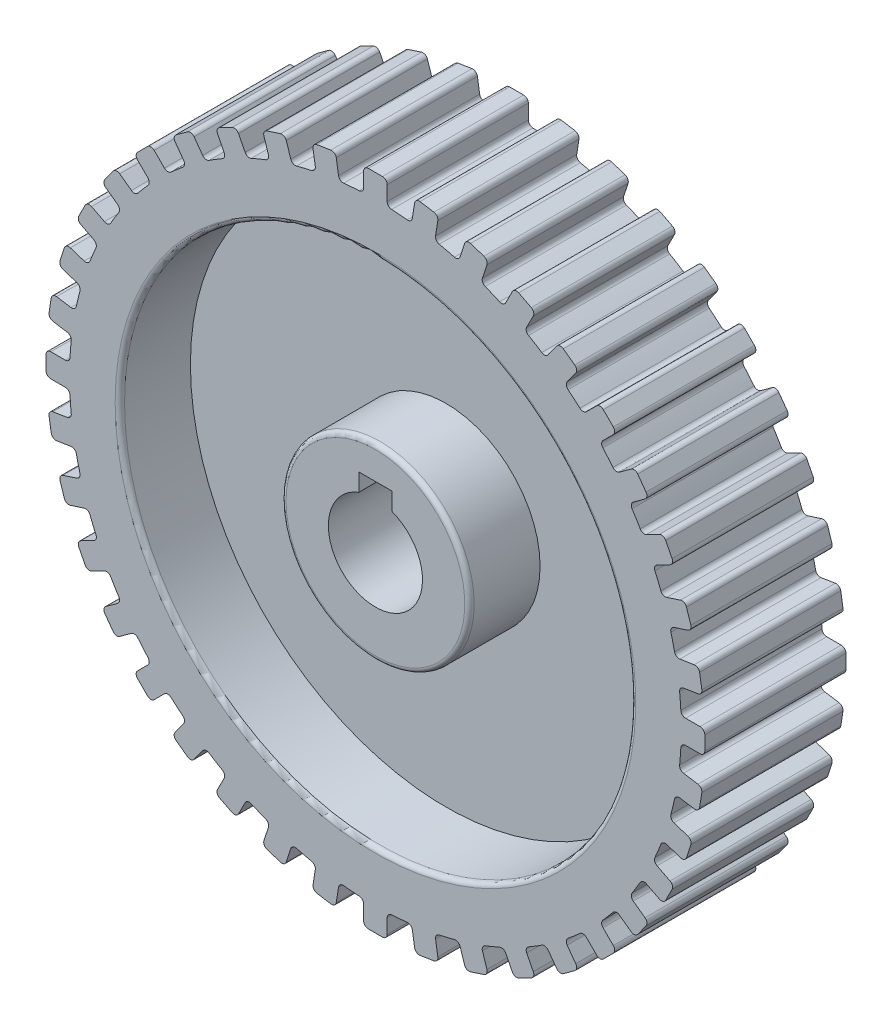
SolidWorks part; units mm, degrees
ref_plane "Front Plane" through (0, 0, 0) normal (0, 0, 1) x (1, 0, 0)
ref_plane "Top Plane" through (0, 0, 0) normal (0, 1, 0) x (1, 0, 0)
ref_plane "Right Plane" through (0, 0, 0) normal (1, 0, 0) x (0, 0, -1)
sketch "Sketch1" plane through (0, 0, 0) normal (0, 0, 1) x (1, 0, 0)
  line L0 (8.3248, 68.5416) -> (7.8409, 65.4868)
  line L1 (-1.5, 70) -> (1.5, 70)
  line L2 (2.5, 69) -> (2.5, 65.9071)
  line L3 (-2.5, 69) -> (-2.5, 65.9071)
  line L4 (9.4689, 69.3728) -> (12.4319, 68.9035)
  line L5 (13.2632, 67.7594) -> (12.7794, 64.7046)
  line L6 (18.9445, 66.3954) -> (17.9888, 63.4539)
  line L7 (20.2046, 67.0375) -> (23.0578, 66.1104)
  line L8 (23.6998, 64.8504) -> (22.7441, 61.9089)
  line L9 (29.0978, 62.6144) -> (27.6937, 59.8587)
  line L10 (30.4428, 63.0514) -> (33.1158, 61.6895)
  line L11 (33.5529, 60.3445) -> (32.1487, 57.5887)
  line L12 (38.5346, 57.2916) -> (36.7167, 54.7895)
  line L13 (39.9314, 57.5129) -> (42.3585, 55.7495)
  line L14 (42.5797, 54.3527) -> (40.7618, 51.8505)
  line L15 (47.0226, 50.5581) -> (44.8356, 48.3711)
  line L16 (48.4368, 50.5581) -> (50.5581, 48.4368)
  line L17 (50.5581, 47.0226) -> (48.3711, 44.8356)
  line L18 (54.3527, 42.5797) -> (51.8505, 40.7618)
  line L19 (55.7495, 42.3585) -> (57.5129, 39.9314)
  line L20 (57.2916, 38.5346) -> (54.7895, 36.7167)
  line L21 (60.3445, 33.5529) -> (57.5887, 32.1487)
  line L22 (61.6895, 33.1158) -> (63.0514, 30.4428)
  line L23 (62.6144, 29.0978) -> (59.8587, 27.6937)
  line L24 (64.8504, 23.6998) -> (61.9089, 22.7441)
  line L25 (66.1104, 23.0578) -> (67.0375, 20.2046)
  line L26 (66.3954, 18.9445) -> (63.4539, 17.9888)
  line L27 (67.7594, 13.2632) -> (64.7046, 12.7794)
  line L28 (68.9035, 12.4319) -> (69.3728, 9.4689)
  line L29 (68.5416, 8.3248) -> (65.4868, 7.8409)
  line L30 (69, 2.5) -> (65.9071, 2.5)
  line L31 (70, 1.5) -> (70, -1.5)
  line L32 (69, -2.5) -> (65.9071, -2.5)
  line L33 (68.5416, -8.3248) -> (65.4868, -7.8409)
  line L34 (69.3728, -9.4689) -> (68.9035, -12.4319)
  line L35 (67.7594, -13.2632) -> (64.7046, -12.7794)
  line L36 (66.3954, -18.9445) -> (63.4539, -17.9888)
  line L37 (67.0375, -20.2046) -> (66.1104, -23.0578)
  line L38 (64.8504, -23.6998) -> (61.9089, -22.7441)
  line L39 (62.6144, -29.0978) -> (59.8587, -27.6937)
  line L40 (63.0514, -30.4428) -> (61.6895, -33.1158)
  line L41 (60.3445, -33.5529) -> (57.5887, -32.1487)
  line L42 (57.2916, -38.5346) -> (54.7895, -36.7167)
  line L43 (57.5129, -39.9314) -> (55.7495, -42.3585)
  line L44 (54.3527, -42.5797) -> (51.8505, -40.7618)
  line L45 (50.5581, -47.0226) -> (48.3711, -44.8356)
  line L46 (50.5581, -48.4368) -> (48.4368, -50.5581)
  line L47 (47.0226, -50.5581) -> (44.8356, -48.3711)
  line L48 (42.5797, -54.3527) -> (40.7618, -51.8505)
  line L49 (42.3585, -55.7495) -> (39.9314, -57.5129)
  line L50 (38.5346, -57.2916) -> (36.7167, -54.7895)
  line L51 (33.5529, -60.3445) -> (32.1487, -57.5887)
  line L52 (33.1158, -61.6895) -> (30.4428, -63.0514)
  line L53 (29.0978, -62.6144) -> (27.6937, -59.8587)
  line L54 (23.6998, -64.8504) -> (22.7441, -61.9089)
  line L55 (23.0578, -66.1104) -> (20.2046, -67.0375)
  line L56 (18.9445, -66.3954) -> (17.9888, -63.4539)
  line L57 (13.2632, -67.7594) -> (12.7794, -64.7046)
  line L58 (12.4319, -68.9035) -> (9.4689, -69.3728)
  line L59 (8.3248, -68.5416) -> (7.8409, -65.4868)
  line L60 (2.5, -69) -> (2.5, -65.9071)
  line L61 (1.5, -70) -> (-1.5, -70)
  line L62 (-2.5, -69) -> (-2.5, -65.9071)
  line L63 (-8.3248, -68.5416) -> (-7.8409, -65.4868)
  line L64 (-9.4689, -69.3728) -> (-12.4319, -68.9035)
  line L65 (-13.2632, -67.7594) -> (-12.7794, -64.7046)
  line L66 (-18.9445, -66.3954) -> (-17.9888, -63.4539)
  line L67 (-20.2046, -67.0375) -> (-23.0578, -66.1104)
  line L68 (-23.6998, -64.8504) -> (-22.7441, -61.9089)
  line L69 (-29.0978, -62.6144) -> (-27.6937, -59.8587)
  line L70 (-30.4428, -63.0514) -> (-33.1158, -61.6895)
  line L71 (-33.5529, -60.3445) -> (-32.1487, -57.5887)
  line L72 (-38.5346, -57.2916) -> (-36.7167, -54.7895)
  line L73 (-39.9314, -57.5129) -> (-42.3585, -55.7495)
  line L74 (-42.5797, -54.3527) -> (-40.7618, -51.8505)
  line L75 (-47.0226, -50.5581) -> (-44.8356, -48.3711)
  line L76 (-48.4368, -50.5581) -> (-50.5581, -48.4368)
  line L77 (-50.5581, -47.0226) -> (-48.3711, -44.8356)
  line L78 (-54.3527, -42.5797) -> (-51.8505, -40.7618)
  line L79 (-55.7495, -42.3585) -> (-57.5129, -39.9314)
  line L80 (-57.2916, -38.5346) -> (-54.7895, -36.7167)
  line L81 (-60.3445, -33.5529) -> (-57.5887, -32.1487)
  line L82 (-61.6895, -33.1158) -> (-63.0514, -30.4428)
  line L83 (-62.6144, -29.0978) -> (-59.8587, -27.6937)
  line L84 (-64.8504, -23.6998) -> (-61.9089, -22.7441)
  line L85 (-66.1104, -23.0578) -> (-67.0375, -20.2046)
  line L86 (-66.3954, -18.9445) -> (-63.4539, -17.9888)
  line L87 (-67.7594, -13.2632) -> (-64.7046, -12.7794)
  line L88 (-68.9035, -12.4319) -> (-69.3728, -9.4689)
  line L89 (-68.5416, -8.3248) -> (-65.4868, -7.8409)
  line L90 (-69, -2.5) -> (-65.9071, -2.5)
  line L91 (-70, -1.5) -> (-70, 1.5)
  line L92 (-69, 2.5) -> (-65.9071, 2.5)
  line L93 (-68.5416, 8.3248) -> (-65.4868, 7.8409)
  line L94 (-69.3728, 9.4689) -> (-68.9035, 12.4319)
  line L95 (-67.7594, 13.2632) -> (-64.7046, 12.7794)
  line L96 (-66.3954, 18.9445) -> (-63.4539, 17.9888)
  line L97 (-67.0375, 20.2046) -> (-66.1104, 23.0578)
  line L98 (-64.8504, 23.6998) -> (-61.9089, 22.7441)
  line L99 (-62.6144, 29.0978) -> (-59.8587, 27.6937)
  line L100 (-63.0514, 30.4428) -> (-61.6895, 33.1158)
  line L101 (-60.3445, 33.5529) -> (-57.5887, 32.1487)
  line L102 (-57.2916, 38.5346) -> (-54.7895, 36.7167)
  line L103 (-57.5129, 39.9314) -> (-55.7495, 42.3585)
  line L104 (-54.3527, 42.5797) -> (-51.8505, 40.7618)
  line L105 (-50.5581, 47.0226) -> (-48.3711, 44.8356)
  line L106 (-50.5581, 48.4368) -> (-48.4368, 50.5581)
  line L107 (-47.0226, 50.5581) -> (-44.8356, 48.3711)
  line L108 (-42.5797, 54.3527) -> (-40.7618, 51.8505)
  line L109 (-42.3585, 55.7495) -> (-39.9314, 57.5129)
  line L110 (-38.5346, 57.2916) -> (-36.7167, 54.7895)
  line L111 (-33.5529, 60.3445) -> (-32.1487, 57.5887)
  line L112 (-33.1158, 61.6895) -> (-30.4428, 63.0514)
  line L113 (-29.0978, 62.6144) -> (-27.6937, 59.8587)
  line L114 (-23.6998, 64.8504) -> (-22.7441, 61.9089)
  line L115 (-23.0578, 66.1104) -> (-20.2046, 67.0375)
  line L116 (-18.9445, 66.3954) -> (-17.9888, 63.4539)
  line L117 (-13.2632, 67.7594) -> (-12.7794, 64.7046)
  line L118 (-12.4319, 68.9035) -> (-9.4689, 69.3728)
  line L119 (-8.3248, 68.5416) -> (-7.8409, 65.4868)
  arc A0 (-3.447, 64.9085) -> (-6.7494, 64.6486) centre (0, 0) ccw
  arc A2 (-2.5, 65.9071) -> (-3.447, 64.9085) centre (-3.5, 65.9071) cw
  arc A3 (3.447, 64.9085) -> (2.5, 65.9071) centre (3.5, 65.9071) cw
  arc A4 (1.5, 70) -> (2.5, 69) centre (1.5, 69) cw
  arc A5 (-1.5, 70) -> (-2.5, 69) centre (-1.5, 69) ccw
  arc A6 (7.8409, 65.4868) -> (6.7494, 64.6486) centre (6.8532, 65.6432) cw
  arc A7 (9.4689, 69.3728) -> (8.3248, 68.5416) centre (9.3124, 68.3851) ccw
  arc A8 (12.4319, 68.9035) -> (13.2632, 67.7594) centre (12.2755, 67.9158) cw
  arc A9 (13.5585, 63.5702) -> (12.7794, 64.7046) centre (13.7671, 64.5482) cw
  arc A10 (17.9888, 63.4539) -> (16.7796, 62.7969) centre (17.0377, 63.763) cw
  arc A11 (20.2046, 67.0375) -> (18.9445, 66.3954) centre (19.8956, 66.0864) ccw
  arc A12 (23.0578, 66.1104) -> (23.6998, 64.8504) centre (22.7488, 65.1594) cw
  arc A13 (23.3361, 60.6665) -> (22.7441, 61.9089) centre (23.6951, 61.5998) cw
  arc A14 (27.6937, 59.8587) -> (26.3966, 59.3988) centre (26.8027, 60.3127) cw
  arc A15 (30.4428, 63.0514) -> (29.0978, 62.6144) centre (29.9888, 62.1604) ccw
  arc A16 (33.1158, 61.6895) -> (33.5529, 60.3445) centre (32.6619, 60.7985) cw
  arc A17 (32.5391, 56.269) -> (32.1487, 57.5887) centre (33.0397, 57.1347) cw
  arc A18 (36.7167, 54.7895) -> (35.3636, 54.5382) centre (35.9077, 55.3772) cw
  arc A19 (39.9314, 57.5129) -> (38.5346, 57.2916) centre (39.3437, 56.7039) ccw
  arc A20 (42.3585, 55.7495) -> (42.5797, 54.3527) centre (41.7707, 54.9405) cw
  arc A21 (40.9409, 50.486) -> (40.7618, 51.8505) centre (41.5708, 51.2627) cw
  arc A22 (44.8356, 48.3711) -> (43.4599, 48.3346) centre (44.1285, 49.0783) cw
  arc A23 (48.4368, 50.5581) -> (47.0226, 50.5581) centre (47.7297, 49.851) ccw
  arc A24 (50.5581, 48.4368) -> (50.5581, 47.0226) centre (49.851, 47.7297) cw
  arc A25 (48.3346, 43.4599) -> (48.3711, 44.8356) centre (49.0783, 44.1285) cw
  arc A26 (51.8505, 40.7618) -> (50.486, 40.9409) centre (51.2627, 41.5708) cw
  arc A27 (55.7495, 42.3585) -> (54.3527, 42.5797) centre (54.9405, 41.7707) ccw
  arc A28 (57.5129, 39.9314) -> (57.2916, 38.5346) centre (56.7039, 39.3437) cw
  arc A29 (54.5382, 35.3636) -> (54.7895, 36.7167) centre (55.3772, 35.9077) cw
  arc A30 (57.5887, 32.1487) -> (56.269, 32.5391) centre (57.1347, 33.0397) cw
  arc A31 (61.6895, 33.1158) -> (60.3445, 33.5529) centre (60.7985, 32.6619) ccw
  arc A32 (63.0514, 30.4428) -> (62.6144, 29.0978) centre (62.1604, 29.9888) cw
  arc A33 (59.3988, 26.3966) -> (59.8587, 27.6937) centre (60.3127, 26.8027) cw
  arc A34 (61.9089, 22.7441) -> (60.6665, 23.3361) centre (61.5998, 23.6951) cw
  arc A35 (66.1104, 23.0578) -> (64.8504, 23.6998) centre (65.1594, 22.7488) ccw
  arc A36 (67.0375, 20.2046) -> (66.3954, 18.9445) centre (66.0864, 19.8956) cw
  arc A37 (62.7969, 16.7796) -> (63.4539, 17.9888) centre (63.763, 17.0377) cw
  arc A38 (64.7046, 12.7794) -> (63.5702, 13.5585) centre (64.5482, 13.7671) cw
  arc A39 (68.9035, 12.4319) -> (67.7594, 13.2632) centre (67.9158, 12.2755) ccw
  arc A40 (69.3728, 9.4689) -> (68.5416, 8.3248) centre (68.3851, 9.3124) cw
  arc A41 (64.6486, 6.7494) -> (65.4868, 7.8409) centre (65.6432, 6.8532) cw
  arc A42 (65.9071, 2.5) -> (64.9085, 3.447) centre (65.9071, 3.5) cw
  arc A43 (70, 1.5) -> (69, 2.5) centre (69, 1.5) ccw
  arc A44 (70, -1.5) -> (69, -2.5) centre (69, -1.5) cw
  arc A45 (64.9085, -3.447) -> (65.9071, -2.5) centre (65.9071, -3.5) cw
  arc A46 (65.4868, -7.8409) -> (64.6486, -6.7494) centre (65.6432, -6.8532) cw
  arc A47 (69.3728, -9.4689) -> (68.5416, -8.3248) centre (68.3851, -9.3124) ccw
  arc A48 (68.9035, -12.4319) -> (67.7594, -13.2632) centre (67.9158, -12.2755) cw
  arc A49 (63.5702, -13.5585) -> (64.7046, -12.7794) centre (64.5482, -13.7671) cw
  arc A50 (63.4539, -17.9888) -> (62.7969, -16.7796) centre (63.763, -17.0377) cw
  arc A51 (67.0375, -20.2046) -> (66.3954, -18.9445) centre (66.0864, -19.8956) ccw
  arc A52 (66.1104, -23.0578) -> (64.8504, -23.6998) centre (65.1594, -22.7488) cw
  arc A53 (60.6665, -23.3361) -> (61.9089, -22.7441) centre (61.5998, -23.6951) cw
  arc A54 (59.8587, -27.6937) -> (59.3988, -26.3966) centre (60.3127, -26.8027) cw
  arc A55 (63.0514, -30.4428) -> (62.6144, -29.0978) centre (62.1604, -29.9888) ccw
  arc A56 (61.6895, -33.1158) -> (60.3445, -33.5529) centre (60.7985, -32.6619) cw
  arc A57 (56.269, -32.5391) -> (57.5887, -32.1487) centre (57.1347, -33.0397) cw
  arc A58 (54.7895, -36.7167) -> (54.5382, -35.3636) centre (55.3772, -35.9077) cw
  arc A59 (57.5129, -39.9314) -> (57.2916, -38.5346) centre (56.7039, -39.3437) ccw
  arc A60 (55.7495, -42.3585) -> (54.3527, -42.5797) centre (54.9405, -41.7707) cw
  arc A61 (50.486, -40.9409) -> (51.8505, -40.7618) centre (51.2627, -41.5708) cw
  arc A62 (48.3711, -44.8356) -> (48.3346, -43.4599) centre (49.0783, -44.1285) cw
  arc A63 (50.5581, -48.4368) -> (50.5581, -47.0226) centre (49.851, -47.7297) ccw
  arc A64 (48.4368, -50.5581) -> (47.0226, -50.5581) centre (47.7297, -49.851) cw
  arc A65 (43.4599, -48.3346) -> (44.8356, -48.3711) centre (44.1285, -49.0783) cw
  arc A66 (40.7618, -51.8505) -> (40.9409, -50.486) centre (41.5708, -51.2627) cw
  arc A67 (42.3585, -55.7495) -> (42.5797, -54.3527) centre (41.7707, -54.9405) ccw
  arc A68 (39.9314, -57.5129) -> (38.5346, -57.2916) centre (39.3437, -56.7039) cw
  arc A69 (35.3636, -54.5382) -> (36.7167, -54.7895) centre (35.9077, -55.3772) cw
  arc A70 (32.1487, -57.5887) -> (32.5391, -56.269) centre (33.0397, -57.1347) cw
  arc A71 (33.1158, -61.6895) -> (33.5529, -60.3445) centre (32.6619, -60.7985) ccw
  arc A72 (30.4428, -63.0514) -> (29.0978, -62.6144) centre (29.9888, -62.1604) cw
  arc A73 (26.3966, -59.3988) -> (27.6937, -59.8587) centre (26.8027, -60.3127) cw
  arc A74 (22.7441, -61.9089) -> (23.3361, -60.6665) centre (23.6951, -61.5998) cw
  arc A75 (23.0578, -66.1104) -> (23.6998, -64.8504) centre (22.7488, -65.1594) ccw
  arc A76 (20.2046, -67.0375) -> (18.9445, -66.3954) centre (19.8956, -66.0864) cw
  arc A77 (16.7796, -62.7969) -> (17.9888, -63.4539) centre (17.0377, -63.763) cw
  arc A78 (12.7794, -64.7046) -> (13.5585, -63.5702) centre (13.7671, -64.5482) cw
  arc A79 (12.4319, -68.9035) -> (13.2632, -67.7594) centre (12.2755, -67.9158) ccw
  arc A80 (9.4689, -69.3728) -> (8.3248, -68.5416) centre (9.3124, -68.3851) cw
  arc A81 (6.7494, -64.6486) -> (7.8409, -65.4868) centre (6.8532, -65.6432) cw
  arc A82 (2.5, -65.9071) -> (3.447, -64.9085) centre (3.5, -65.9071) cw
  arc A83 (1.5, -70) -> (2.5, -69) centre (1.5, -69) ccw
  arc A84 (-1.5, -70) -> (-2.5, -69) centre (-1.5, -69) cw
  arc A85 (-3.447, -64.9085) -> (-2.5, -65.9071) centre (-3.5, -65.9071) cw
  arc A86 (-7.8409, -65.4868) -> (-6.7494, -64.6486) centre (-6.8532, -65.6432) cw
  arc A87 (-9.4689, -69.3728) -> (-8.3248, -68.5416) centre (-9.3124, -68.3851) ccw
  arc A88 (-12.4319, -68.9035) -> (-13.2632, -67.7594) centre (-12.2755, -67.9158) cw
  arc A89 (-13.5585, -63.5702) -> (-12.7794, -64.7046) centre (-13.7671, -64.5482) cw
  arc A90 (-17.9888, -63.4539) -> (-16.7796, -62.7969) centre (-17.0377, -63.763) cw
  arc A91 (-20.2046, -67.0375) -> (-18.9445, -66.3954) centre (-19.8956, -66.0864) ccw
  arc A92 (-23.0578, -66.1104) -> (-23.6998, -64.8504) centre (-22.7488, -65.1594) cw
  arc A93 (-23.3361, -60.6665) -> (-22.7441, -61.9089) centre (-23.6951, -61.5998) cw
  arc A94 (-27.6937, -59.8587) -> (-26.3966, -59.3988) centre (-26.8027, -60.3127) cw
  arc A95 (-30.4428, -63.0514) -> (-29.0978, -62.6144) centre (-29.9888, -62.1604) ccw
  arc A96 (-33.1158, -61.6895) -> (-33.5529, -60.3445) centre (-32.6619, -60.7985) cw
  arc A97 (-32.5391, -56.269) -> (-32.1487, -57.5887) centre (-33.0397, -57.1347) cw
  arc A98 (-36.7167, -54.7895) -> (-35.3636, -54.5382) centre (-35.9077, -55.3772) cw
  arc A99 (-39.9314, -57.5129) -> (-38.5346, -57.2916) centre (-39.3437, -56.7039) ccw
  arc A100 (-42.3585, -55.7495) -> (-42.5797, -54.3527) centre (-41.7707, -54.9405) cw
  arc A101 (-40.9409, -50.486) -> (-40.7618, -51.8505) centre (-41.5708, -51.2627) cw
  arc A102 (-44.8356, -48.3711) -> (-43.4599, -48.3346) centre (-44.1285, -49.0783) cw
  arc A103 (-48.4368, -50.5581) -> (-47.0226, -50.5581) centre (-47.7297, -49.851) ccw
  arc A104 (-50.5581, -48.4368) -> (-50.5581, -47.0226) centre (-49.851, -47.7297) cw
  arc A105 (-48.3346, -43.4599) -> (-48.3711, -44.8356) centre (-49.0783, -44.1285) cw
  arc A106 (-51.8505, -40.7618) -> (-50.486, -40.9409) centre (-51.2627, -41.5708) cw
  arc A107 (-55.7495, -42.3585) -> (-54.3527, -42.5797) centre (-54.9405, -41.7707) ccw
  arc A108 (-57.5129, -39.9314) -> (-57.2916, -38.5346) centre (-56.7039, -39.3437) cw
  arc A109 (-54.5382, -35.3636) -> (-54.7895, -36.7167) centre (-55.3772, -35.9077) cw
  arc A110 (-57.5887, -32.1487) -> (-56.269, -32.5391) centre (-57.1347, -33.0397) cw
  arc A111 (-61.6895, -33.1158) -> (-60.3445, -33.5529) centre (-60.7985, -32.6619) ccw
  arc A112 (-63.0514, -30.4428) -> (-62.6144, -29.0978) centre (-62.1604, -29.9888) cw
  arc A113 (-59.3988, -26.3966) -> (-59.8587, -27.6937) centre (-60.3127, -26.8027) cw
  arc A114 (-61.9089, -22.7441) -> (-60.6665, -23.3361) centre (-61.5998, -23.6951) cw
  arc A115 (-66.1104, -23.0578) -> (-64.8504, -23.6998) centre (-65.1594, -22.7488) ccw
  arc A116 (-67.0375, -20.2046) -> (-66.3954, -18.9445) centre (-66.0864, -19.8956) cw
  arc A117 (-62.7969, -16.7796) -> (-63.4539, -17.9888) centre (-63.763, -17.0377) cw
  arc A118 (-64.7046, -12.7794) -> (-63.5702, -13.5585) centre (-64.5482, -13.7671) cw
  arc A119 (-68.9035, -12.4319) -> (-67.7594, -13.2632) centre (-67.9158, -12.2755) ccw
  arc A120 (-69.3728, -9.4689) -> (-68.5416, -8.3248) centre (-68.3851, -9.3124) cw
  arc A121 (-64.6486, -6.7494) -> (-65.4868, -7.8409) centre (-65.6432, -6.8532) cw
  arc A122 (-65.9071, -2.5) -> (-64.9085, -3.447) centre (-65.9071, -3.5) cw
  arc A123 (-70, -1.5) -> (-69, -2.5) centre (-69, -1.5) ccw
  arc A124 (-70, 1.5) -> (-69, 2.5) centre (-69, 1.5) cw
  arc A125 (-64.9085, 3.447) -> (-65.9071, 2.5) centre (-65.9071, 3.5) cw
  arc A126 (-65.4868, 7.8409) -> (-64.6486, 6.7494) centre (-65.6432, 6.8532) cw
  arc A127 (-69.3728, 9.4689) -> (-68.5416, 8.3248) centre (-68.3851, 9.3124) ccw
  arc A128 (-68.9035, 12.4319) -> (-67.7594, 13.2632) centre (-67.9158, 12.2755) cw
  arc A129 (-63.5702, 13.5585) -> (-64.7046, 12.7794) centre (-64.5482, 13.7671) cw
  arc A130 (-63.4539, 17.9888) -> (-62.7969, 16.7796) centre (-63.763, 17.0377) cw
  arc A131 (-67.0375, 20.2046) -> (-66.3954, 18.9445) centre (-66.0864, 19.8956) ccw
  arc A132 (-66.1104, 23.0578) -> (-64.8504, 23.6998) centre (-65.1594, 22.7488) cw
  arc A133 (-60.6665, 23.3361) -> (-61.9089, 22.7441) centre (-61.5998, 23.6951) cw
  arc A134 (-59.8587, 27.6937) -> (-59.3988, 26.3966) centre (-60.3127, 26.8027) cw
  arc A135 (-63.0514, 30.4428) -> (-62.6144, 29.0978) centre (-62.1604, 29.9888) ccw
  arc A136 (-61.6895, 33.1158) -> (-60.3445, 33.5529) centre (-60.7985, 32.6619) cw
  arc A137 (-56.269, 32.5391) -> (-57.5887, 32.1487) centre (-57.1347, 33.0397) cw
  arc A138 (-54.7895, 36.7167) -> (-54.5382, 35.3636) centre (-55.3772, 35.9077) cw
  arc A139 (-57.5129, 39.9314) -> (-57.2916, 38.5346) centre (-56.7039, 39.3437) ccw
  arc A140 (-55.7495, 42.3585) -> (-54.3527, 42.5797) centre (-54.9405, 41.7707) cw
  arc A141 (-50.486, 40.9409) -> (-51.8505, 40.7618) centre (-51.2627, 41.5708) cw
  arc A142 (-48.3711, 44.8356) -> (-48.3346, 43.4599) centre (-49.0783, 44.1285) cw
  arc A143 (-50.5581, 48.4368) -> (-50.5581, 47.0226) centre (-49.851, 47.7297) ccw
  arc A144 (-48.4368, 50.5581) -> (-47.0226, 50.5581) centre (-47.7297, 49.851) cw
  arc A145 (-43.4599, 48.3346) -> (-44.8356, 48.3711) centre (-44.1285, 49.0783) cw
  arc A146 (-40.7618, 51.8505) -> (-40.9409, 50.486) centre (-41.5708, 51.2627) cw
  arc A147 (-42.3585, 55.7495) -> (-42.5797, 54.3527) centre (-41.7707, 54.9405) ccw
  arc A148 (-39.9314, 57.5129) -> (-38.5346, 57.2916) centre (-39.3437, 56.7039) cw
  arc A149 (-35.3636, 54.5382) -> (-36.7167, 54.7895) centre (-35.9077, 55.3772) cw
  arc A150 (-32.1487, 57.5887) -> (-32.5391, 56.269) centre (-33.0397, 57.1347) cw
  arc A151 (-33.1158, 61.6895) -> (-33.5529, 60.3445) centre (-32.6619, 60.7985) ccw
  arc A152 (-30.4428, 63.0514) -> (-29.0978, 62.6144) centre (-29.9888, 62.1604) cw
  arc A153 (-26.3966, 59.3988) -> (-27.6937, 59.8587) centre (-26.8027, 60.3127) cw
  arc A154 (-22.7441, 61.9089) -> (-23.3361, 60.6665) centre (-23.6951, 61.5998) cw
  arc A155 (-23.0578, 66.1104) -> (-23.6998, 64.8504) centre (-22.7488, 65.1594) ccw
  arc A156 (-20.2046, 67.0375) -> (-18.9445, 66.3954) centre (-19.8956, 66.0864) cw
  arc A157 (-16.7796, 62.7969) -> (-17.9888, 63.4539) centre (-17.0377, 63.763) cw
  arc A158 (-12.7794, 64.7046) -> (-13.5585, 63.5702) centre (-13.7671, 64.5482) cw
  arc A159 (-12.4319, 68.9035) -> (-13.2632, 67.7594) centre (-12.2755, 67.9158) ccw
  arc A160 (-9.4689, 69.3728) -> (-8.3248, 68.5416) centre (-9.3124, 68.3851) cw
  arc A161 (-6.7494, 64.6486) -> (-7.8409, 65.4868) centre (-6.8532, 65.6432) cw
  arc A162 (-13.5585, 63.5702) -> (-16.7796, 62.7969) centre (0, 0) ccw
  arc A163 (6.7494, 64.6486) -> (3.447, 64.9085) centre (0, 0) ccw
  arc A164 (16.7796, 62.7969) -> (13.5585, 63.5702) centre (0, 0) ccw
  arc A165 (26.3966, 59.3988) -> (23.3361, 60.6665) centre (0, 0) ccw
  arc A166 (-23.3361, 60.6665) -> (-26.3966, 59.3988) centre (0, 0) ccw
  arc A167 (-32.5391, 56.269) -> (-35.3636, 54.5382) centre (0, 0) ccw
  arc A168 (-40.9409, 50.486) -> (-43.4599, 48.3346) centre (0, 0) ccw
  arc A169 (-48.3346, 43.4599) -> (-50.486, 40.9409) centre (0, 0) ccw
  arc A170 (-54.5382, 35.3636) -> (-56.269, 32.5391) centre (0, 0) ccw
  arc A171 (35.3636, 54.5382) -> (32.5391, 56.269) centre (0, 0) ccw
  arc A172 (43.4599, 48.3346) -> (40.9409, 50.486) centre (0, 0) ccw
  arc A173 (50.486, 40.9409) -> (48.3346, 43.4599) centre (0, 0) ccw
  arc A174 (56.269, 32.5391) -> (54.5382, 35.3636) centre (0, 0) ccw
  arc A175 (60.6665, 23.3361) -> (59.3988, 26.3966) centre (0, 0) ccw
  arc A176 (63.5702, 13.5585) -> (62.7969, 16.7796) centre (0, 0) ccw
  arc A177 (64.9085, 3.447) -> (64.6486, 6.7494) centre (0, 0) ccw
  arc A178 (64.6486, -6.7494) -> (64.9085, -3.447) centre (0, 0) ccw
  arc A179 (62.7969, -16.7796) -> (63.5702, -13.5585) centre (0, 0) ccw
  arc A180 (59.3988, -26.3966) -> (60.6665, -23.3361) centre (0, 0) ccw
  arc A181 (54.5382, -35.3636) -> (56.269, -32.5391) centre (0, 0) ccw
  arc A182 (48.3346, -43.4599) -> (50.486, -40.9409) centre (0, 0) ccw
  arc A183 (40.9409, -50.486) -> (43.4599, -48.3346) centre (0, 0) ccw
  arc A184 (32.5391, -56.269) -> (35.3636, -54.5382) centre (0, 0) ccw
  arc A185 (23.3361, -60.6665) -> (26.3966, -59.3988) centre (0, 0) ccw
  arc A186 (13.5585, -63.5702) -> (16.7796, -62.7969) centre (0, 0) ccw
  arc A187 (3.447, -64.9085) -> (6.7494, -64.6486) centre (0, 0) ccw
  arc A188 (-6.7494, -64.6486) -> (-3.447, -64.9085) centre (0, 0) ccw
  arc A189 (-16.7796, -62.7969) -> (-13.5585, -63.5702) centre (0, 0) ccw
  arc A190 (-26.3966, -59.3988) -> (-23.3361, -60.6665) centre (0, 0) ccw
  arc A191 (-35.3636, -54.5382) -> (-32.5391, -56.269) centre (0, 0) ccw
  arc A192 (-43.4599, -48.3346) -> (-40.9409, -50.486) centre (0, 0) ccw
  arc A193 (-50.486, -40.9409) -> (-48.3346, -43.4599) centre (0, 0) ccw
  arc A194 (-56.269, -32.5391) -> (-54.5382, -35.3636) centre (0, 0) ccw
  arc A195 (-60.6665, -23.3361) -> (-59.3988, -26.3966) centre (0, 0) ccw
  arc A196 (-63.5702, -13.5585) -> (-62.7969, -16.7796) centre (0, 0) ccw
  arc A197 (-64.9085, -3.447) -> (-64.6486, -6.7494) centre (0, 0) ccw
  arc A198 (-64.6486, 6.7494) -> (-64.9085, 3.447) centre (0, 0) ccw
  arc A199 (-62.7969, 16.7796) -> (-63.5702, 13.5585) centre (0, 0) ccw
  arc A200 (-59.3988, 26.3966) -> (-60.6665, 23.3361) centre (0, 0) ccw
  point P486 (0, 0)
  dimension "D1" = 1
  dimension "D2" = 40
extrude "Boss-Extrude1" add sketch "Sketch1" along normal blind 30
sketch "Sketch2" plane through (0, 0, 30) normal (0, 0, 1) x (1, 0, 0)
  line L1 (-3.5387, 13.1147) -> (3.5387, 13.1147)
  line L2 (-3.5387, 13.1147) -> (-3.5387, 9.353)
  line L4 (3.5387, 13.1147) -> (3.5387, 9.353)
  circle A0 centre (0, 0) radius 20
  arc A1 (-3.5387, 9.353) -> (3.5387, 9.353) centre (0, 0) ccw
extrude "Cut-Extrude1" cut sketch "Sketch2" against normal blind 30 contours A1 L4 L1 L2
sketch "Sketch3" plane through (0, 0, 30) normal (0, 0, 1) x (1, 0, 0)
  circle A0 centre (0, 0) radius 20
  circle A1 centre (0, 0) radius 54.3215
extrude "Cut-Extrude2" cut sketch "Sketch3" against normal blind 15
fillet "Fillet2" radius 1 1 edges at (54.3215, 0, 30)
fillet "Fillet3" radius 1 1 edges at (20, 0, 30)
